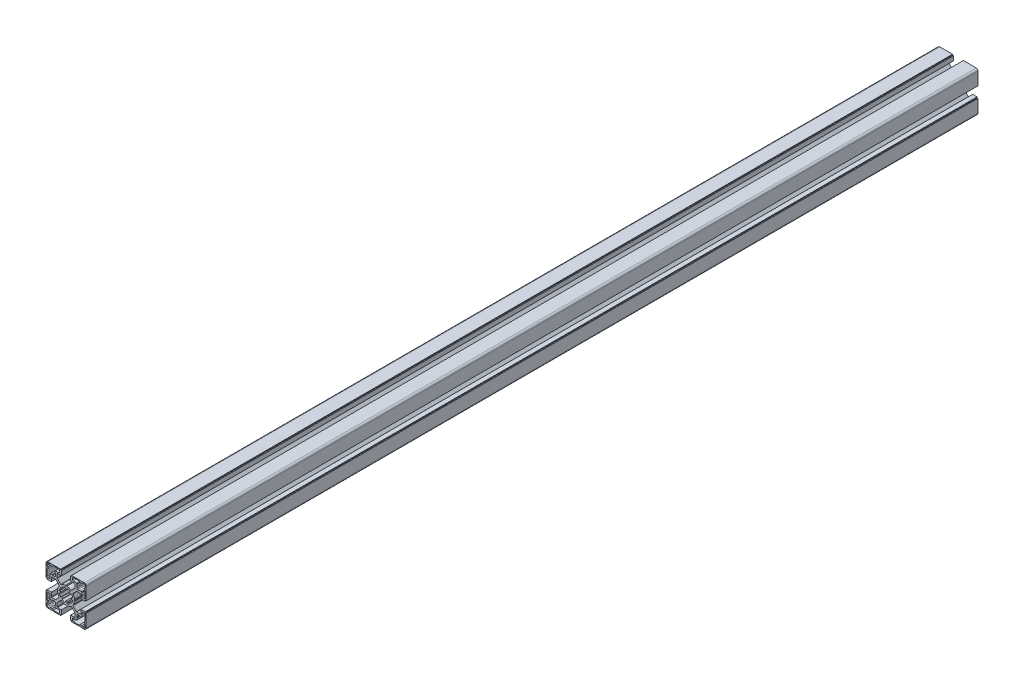
SolidWorks part; units mm, degrees
ref_plane "前视基准面" through (0, 0, 0) normal (0, 0, 1) x (1, 0, 0)
ref_plane "上视基准面" through (0, 0, 0) normal (0, 1, 0) x (1, 0, 0)
ref_plane "右视基准面" through (0, 0, 0) normal (1, 0, 0) x (0, 0, -1)
sketch "草图1" plane through (0, 0, 0) normal (0, 0, 1) x (1, 0, 0)
  line L16 (31.3495, 47.5482) -> (29.8624, 47.744)
  line L17 (28.6738, 44.8745) -> (29.8638, 43.9614)
  line L18 (28.4794, 42.577) -> (27.5663, 43.767)
  line L19 (24.6968, 42.5784) -> (24.8926, 41.0913)
  line L20 (22.9347, 41.0913) -> (23.1305, 42.5784)
  line L21 (20.2611, 43.767) -> (19.348, 42.577)
  line L22 (17.9635, 43.9614) -> (19.1536, 44.8745)
  line L23 (17.965, 47.744) -> (16.4779, 47.5482)
  line L24 (16.4779, 49.5061) -> (17.965, 49.3103)
  line L25 (19.1536, 52.1797) -> (17.9635, 53.0928)
  line L26 (19.348, 54.4773) -> (20.2611, 53.2872)
  line L27 (23.1305, 54.4758) -> (22.9347, 55.9629)
  line L28 (24.8926, 55.9629) -> (24.6968, 54.4758)
  line L29 (27.5663, 53.2872) -> (28.4794, 54.4773)
  line L30 (29.8638, 53.0928) -> (28.6738, 52.1797)
  line L31 (29.8624, 49.3103) -> (31.3495, 49.5061)
  line L32 (11.9137, 66.5271) -> (15.8137, 66.5271)
  line L33 (11.4137, 66.0271) -> (11.9137, 66.5271)
  line L34 (11.4137, 64.0271) -> (11.4137, 66.0271)
  line L35 (11.9137, 63.5271) -> (11.4137, 64.0271)
  line L36 (11.9137, 61.5271) -> (11.9137, 63.5271)
  line L37 (8.9137, 60.5271) -> (10.9137, 60.5271)
  line L38 (8.4137, 61.0271) -> (8.9137, 60.5271)
  line L39 (6.4137, 61.0271) -> (8.4137, 61.0271)
  line L40 (5.9137, 60.5271) -> (6.4137, 61.0271)
  line L41 (5.9137, 56.6271) -> (5.9137, 60.5271)
  line L42 (3.4137, 55.6271) -> (4.9137, 55.6271)
  line L43 (2.4137, 63.0271) -> (2.4137, 56.6271)
  line L44 (3.4137, 64.0271) -> (2.4137, 63.0271)
  line L45 (3.4137, 66.0271) -> (3.4137, 64.0271)
  line L46 (2.4137, 67.0271) -> (3.4137, 66.0271)
  line L47 (2.4137, 69.0271) -> (2.4137, 67.0271)
  line L48 (5.4137, 70.0271) -> (3.4137, 70.0271)
  line L49 (6.4137, 69.0271) -> (5.4137, 70.0271)
  line L50 (8.4137, 69.0271) -> (6.4137, 69.0271)
  line L51 (9.4137, 70.0271) -> (8.4137, 69.0271)
  line L52 (15.8137, 70.0271) -> (9.4137, 70.0271)
  line L53 (16.8137, 67.5271) -> (16.8137, 69.0271)
  line L54 (42.9137, 55.6271) -> (44.4137, 55.6271)
  line L55 (41.9137, 60.5271) -> (41.9137, 56.6271)
  line L56 (41.4137, 61.0271) -> (41.9137, 60.5271)
  line L57 (39.4137, 61.0271) -> (41.4137, 61.0271)
  line L58 (38.9137, 60.5271) -> (39.4137, 61.0271)
  line L59 (36.9137, 60.5271) -> (38.9137, 60.5271)
  line L60 (35.9137, 63.5271) -> (35.9137, 61.5271)
  line L61 (36.4137, 64.0271) -> (35.9137, 63.5271)
  line L62 (36.4137, 66.0271) -> (36.4137, 64.0271)
  line L63 (35.9137, 66.5271) -> (36.4137, 66.0271)
  line L64 (32.0137, 66.5271) -> (35.9137, 66.5271)
  line L65 (31.0137, 69.0271) -> (31.0137, 67.5271)
  line L66 (38.4137, 70.0271) -> (32.0137, 70.0271)
  line L67 (39.4137, 69.0271) -> (38.4137, 70.0271)
  line L68 (41.4137, 69.0271) -> (39.4137, 69.0271)
  line L69 (42.4137, 70.0271) -> (41.4137, 69.0271)
  line L70 (44.4137, 70.0271) -> (42.4137, 70.0271)
  line L71 (45.4137, 67.0271) -> (45.4137, 69.0271)
  line L72 (44.4137, 66.0271) -> (45.4137, 67.0271)
  line L73 (44.4137, 64.0271) -> (44.4137, 66.0271)
  line L74 (45.4137, 63.0271) -> (44.4137, 64.0271)
  line L75 (45.4137, 56.6271) -> (45.4137, 63.0271)
  line L76 (4.9137, 41.4271) -> (3.4137, 41.4271)
  line L77 (5.9137, 36.5271) -> (5.9137, 40.4271)
  line L78 (6.4137, 36.0271) -> (5.9137, 36.5271)
  line L79 (8.4137, 36.0271) -> (6.4137, 36.0271)
  line L80 (8.9137, 36.5271) -> (8.4137, 36.0271)
  line L81 (10.9137, 36.5271) -> (8.9137, 36.5271)
  line L82 (11.9137, 33.5271) -> (11.9137, 35.5271)
  line L83 (11.4137, 33.0271) -> (11.9137, 33.5271)
  line L84 (11.4137, 31.0271) -> (11.4137, 33.0271)
  line L85 (11.9137, 30.5271) -> (11.4137, 31.0271)
  line L86 (15.8137, 30.5271) -> (11.9137, 30.5271)
  line L87 (16.8137, 28.0271) -> (16.8137, 29.5271)
  line L88 (9.4137, 27.0271) -> (15.8137, 27.0271)
  line L89 (8.4137, 28.0271) -> (9.4137, 27.0271)
  line L90 (6.4137, 28.0271) -> (8.4137, 28.0271)
  line L91 (5.4137, 27.0271) -> (6.4137, 28.0271)
  line L92 (3.4137, 27.0271) -> (5.4137, 27.0271)
  line L93 (2.4137, 30.0271) -> (2.4137, 28.0271)
  line L94 (3.4137, 31.0271) -> (2.4137, 30.0271)
  line L95 (3.4137, 33.0271) -> (3.4137, 31.0271)
  line L96 (2.4137, 34.0271) -> (3.4137, 33.0271)
  line L97 (2.4137, 40.4271) -> (2.4137, 34.0271)
  line L98 (45.4137, 34.0271) -> (45.4137, 40.4271)
  line L99 (44.4137, 33.0271) -> (45.4137, 34.0271)
  line L100 (44.4137, 31.0271) -> (44.4137, 33.0271)
  line L101 (45.4137, 30.0271) -> (44.4137, 31.0271)
  line L102 (45.4137, 28.0271) -> (45.4137, 30.0271)
  line L103 (42.4137, 27.0271) -> (44.4137, 27.0271)
  line L104 (41.4137, 28.0271) -> (42.4137, 27.0271)
  line L105 (39.4137, 28.0271) -> (41.4137, 28.0271)
  line L106 (38.4137, 27.0271) -> (39.4137, 28.0271)
  line L107 (32.0137, 27.0271) -> (38.4137, 27.0271)
  line L108 (31.0137, 29.5271) -> (31.0137, 28.0271)
  line L109 (35.9137, 30.5271) -> (32.0137, 30.5271)
  line L110 (36.4137, 31.0271) -> (35.9137, 30.5271)
  line L111 (36.4137, 33.0271) -> (36.4137, 31.0271)
  line L112 (35.9137, 33.5271) -> (36.4137, 33.0271)
  line L113 (35.9137, 35.5271) -> (35.9137, 33.5271)
  line L114 (38.9137, 36.5271) -> (36.9137, 36.5271)
  line L115 (39.4137, 36.0271) -> (38.9137, 36.5271)
  line L116 (41.4137, 36.0271) -> (39.4137, 36.0271)
  line L117 (41.9137, 36.5271) -> (41.4137, 36.0271)
  line L118 (41.9137, 40.4271) -> (41.9137, 36.5271)
  line L119 (44.4137, 41.4271) -> (42.9137, 41.4271)
  line L120 (32.9137, 48.5271) -> (33.3794, 47.7205)
  line L121 (33.3794, 49.3337) -> (32.9137, 48.5271)
  line L122 (35.535, 58.3807) -> (31.7595, 54.6052)
  line L123 (39.9137, 58.5271) -> (35.8886, 58.5271)
  line L124 (40.4137, 53.6271) -> (40.4137, 58.0271)
  line L125 (45.4137, 53.6271) -> (40.4137, 53.6271)
  line L126 (45.4137, 54.6271) -> (45.4137, 53.6271)
  line L127 (46.4137, 54.6271) -> (45.4137, 54.6271)
  line L128 (46.4137, 69.0271) -> (46.4137, 54.6271)
  line L129 (30.0137, 71.0271) -> (44.4137, 71.0271)
  line L130 (30.0137, 70.0271) -> (30.0137, 71.0271)
  line L131 (29.0137, 70.0271) -> (30.0137, 70.0271)
  line L132 (29.0137, 65.0271) -> (29.0137, 70.0271)
  line L133 (33.4137, 65.0271) -> (29.0137, 65.0271)
  line L134 (33.9137, 60.502) -> (33.9137, 64.5271)
  line L135 (29.9918, 56.3729) -> (33.7672, 60.1484)
  line L136 (23.9137, 57.5271) -> (24.7203, 57.9928)
  line L137 (23.1071, 57.9928) -> (23.9137, 57.5271)
  line L138 (14.0601, 60.1484) -> (17.8356, 56.3729)
  line L139 (13.9137, 64.5271) -> (13.9137, 60.502)
  line L140 (18.8137, 65.0271) -> (14.4137, 65.0271)
  line L141 (18.8137, 70.0271) -> (18.8137, 65.0271)
  line L142 (17.8137, 70.0271) -> (18.8137, 70.0271)
  line L143 (17.8137, 71.0271) -> (17.8137, 70.0271)
  line L144 (3.4137, 71.0271) -> (17.8137, 71.0271)
  line L145 (1.4137, 54.6271) -> (1.4137, 69.0271)
  line L146 (2.4137, 54.6271) -> (1.4137, 54.6271)
  line L147 (2.4137, 53.6271) -> (2.4137, 54.6271)
  line L148 (7.4137, 53.6271) -> (2.4137, 53.6271)
  line L149 (7.4137, 58.0271) -> (7.4137, 53.6271)
  line L150 (11.9388, 58.5271) -> (7.9137, 58.5271)
  line L151 (16.0679, 54.6052) -> (12.2924, 58.3807)
  line L152 (14.9137, 48.5271) -> (14.448, 49.3337)
  line L153 (14.448, 47.7205) -> (14.9137, 48.5271)
  line L154 (12.2924, 38.6736) -> (16.0679, 42.449)
  line L155 (7.9137, 38.5271) -> (11.9388, 38.5271)
  line L156 (7.4137, 43.4271) -> (7.4137, 39.0271)
  line L157 (2.4137, 43.4271) -> (7.4137, 43.4271)
  line L158 (2.4137, 42.4271) -> (2.4137, 43.4271)
  line L159 (1.4137, 42.4271) -> (2.4137, 42.4271)
  line L160 (1.4137, 28.0271) -> (1.4137, 42.4271)
  line L161 (17.8137, 26.0271) -> (3.4137, 26.0271)
  line L162 (17.8137, 27.0271) -> (17.8137, 26.0271)
  line L163 (18.8137, 27.0271) -> (17.8137, 27.0271)
  line L164 (18.8137, 32.0271) -> (18.8137, 27.0271)
  line L165 (14.4137, 32.0271) -> (18.8137, 32.0271)
  line L166 (13.9137, 36.5522) -> (13.9137, 32.5271)
  line L167 (17.8356, 40.6813) -> (14.0601, 36.9058)
  line L168 (23.9137, 39.5271) -> (23.1071, 39.0614)
  line L169 (24.7203, 39.0614) -> (23.9137, 39.5271)
  line L170 (33.7672, 36.9058) -> (29.9918, 40.6813)
  line L171 (33.9137, 32.5271) -> (33.9137, 36.5522)
  line L172 (29.0137, 32.0271) -> (33.4137, 32.0271)
  line L173 (29.0137, 27.0271) -> (29.0137, 32.0271)
  line L174 (30.0137, 27.0271) -> (29.0137, 27.0271)
  line L175 (30.0137, 26.0271) -> (30.0137, 27.0271)
  line L176 (44.4137, 26.0271) -> (30.0137, 26.0271)
  line L177 (46.4137, 42.4271) -> (46.4137, 28.0271)
  line L178 (45.4137, 42.4271) -> (46.4137, 42.4271)
  line L179 (45.4137, 43.4271) -> (45.4137, 42.4271)
  line L180 (40.4137, 43.4271) -> (45.4137, 43.4271)
  line L181 (40.4137, 39.0271) -> (40.4137, 43.4271)
  line L182 (35.8886, 38.5271) -> (39.9137, 38.5271)
  line L183 (31.7595, 42.449) -> (35.535, 38.6736)
  arc A0 (29.8624, 47.744) -> (29.8624, 49.3103) centre (23.9137, 48.5271) ccw
  arc A1 (29.8638, 43.9614) -> (31.3495, 47.5482) centre (23.9137, 48.5271) ccw
  arc A2 (27.5663, 43.767) -> (28.6738, 44.8745) centre (23.9137, 48.5271) ccw
  arc A3 (24.8926, 41.0913) -> (28.4794, 42.577) centre (23.9137, 48.5271) ccw
  arc A4 (23.1305, 42.5784) -> (24.6968, 42.5784) centre (23.9137, 48.5271) ccw
  arc A5 (19.348, 42.577) -> (22.9347, 41.0913) centre (23.9137, 48.5271) ccw
  arc A6 (19.1536, 44.8745) -> (20.2611, 43.767) centre (23.9137, 48.5271) ccw
  arc A7 (16.4779, 47.5482) -> (17.9635, 43.9614) centre (23.9137, 48.5271) ccw
  arc A8 (17.965, 49.3103) -> (17.965, 47.744) centre (23.9137, 48.5271) ccw
  arc A9 (17.9635, 53.0928) -> (16.4779, 49.5061) centre (23.9137, 48.5271) ccw
  arc A10 (20.2611, 53.2872) -> (19.1536, 52.1797) centre (23.9137, 48.5271) ccw
  arc A11 (22.9347, 55.9629) -> (19.348, 54.4773) centre (23.9137, 48.5271) ccw
  arc A12 (24.6968, 54.4758) -> (23.1305, 54.4758) centre (23.9137, 48.5271) ccw
  arc A13 (28.4794, 54.4773) -> (24.8926, 55.9629) centre (23.9137, 48.5271) ccw
  arc A14 (28.6738, 52.1797) -> (27.5663, 53.2872) centre (23.9137, 48.5271) ccw
  arc A15 (31.3495, 49.5061) -> (29.8638, 53.0928) centre (23.9137, 48.5271) ccw
  arc A16 (10.9137, 60.5271) -> (11.9137, 61.5271) centre (10.9137, 61.5271) ccw
  arc A17 (4.9137, 55.6271) -> (5.9137, 56.6271) centre (4.9137, 56.6271) ccw
  arc A18 (2.4137, 56.6271) -> (3.4137, 55.6271) centre (3.4137, 56.6271) ccw
  arc A19 (3.4137, 70.0271) -> (2.4137, 69.0271) centre (3.4137, 69.0271) ccw
  arc A20 (16.8137, 69.0271) -> (15.8137, 70.0271) centre (15.8137, 69.0271) ccw
  arc A21 (15.8137, 66.5271) -> (16.8137, 67.5271) centre (15.8137, 67.5271) ccw
  arc A22 (44.4137, 55.6271) -> (45.4137, 56.6271) centre (44.4137, 56.6271) ccw
  arc A23 (41.9137, 56.6271) -> (42.9137, 55.6271) centre (42.9137, 56.6271) ccw
  arc A24 (35.9137, 61.5271) -> (36.9137, 60.5271) centre (36.9137, 61.5271) ccw
  arc A25 (31.0137, 67.5271) -> (32.0137, 66.5271) centre (32.0137, 67.5271) ccw
  arc A26 (32.0137, 70.0271) -> (31.0137, 69.0271) centre (32.0137, 69.0271) ccw
  arc A27 (45.4137, 69.0271) -> (44.4137, 70.0271) centre (44.4137, 69.0271) ccw
  arc A28 (3.4137, 41.4271) -> (2.4137, 40.4271) centre (3.4137, 40.4271) ccw
  arc A29 (5.9137, 40.4271) -> (4.9137, 41.4271) centre (4.9137, 40.4271) ccw
  arc A30 (11.9137, 35.5271) -> (10.9137, 36.5271) centre (10.9137, 35.5271) ccw
  arc A31 (16.8137, 29.5271) -> (15.8137, 30.5271) centre (15.8137, 29.5271) ccw
  arc A32 (15.8137, 27.0271) -> (16.8137, 28.0271) centre (15.8137, 28.0271) ccw
  arc A33 (2.4137, 28.0271) -> (3.4137, 27.0271) centre (3.4137, 28.0271) ccw
  arc A34 (45.4137, 40.4271) -> (44.4137, 41.4271) centre (44.4137, 40.4271) ccw
  arc A35 (44.4137, 27.0271) -> (45.4137, 28.0271) centre (44.4137, 28.0271) ccw
  arc A36 (31.0137, 28.0271) -> (32.0137, 27.0271) centre (32.0137, 28.0271) ccw
  arc A37 (32.0137, 30.5271) -> (31.0137, 29.5271) centre (32.0137, 29.5271) ccw
  arc A38 (36.9137, 36.5271) -> (35.9137, 35.5271) centre (36.9137, 35.5271) ccw
  arc A39 (42.9137, 41.4271) -> (41.9137, 40.4271) centre (42.9137, 40.4271) ccw
  arc A40 (31.7031, 43.0888) -> (31.7595, 42.449) centre (32.1131, 42.8026) ccw
  arc A41 (31.7031, 43.0888) -> (33.3794, 47.7205) centre (23.9137, 48.5271) ccw
  arc A42 (33.3794, 49.3337) -> (31.7031, 53.9654) centre (23.9137, 48.5271) ccw
  arc A43 (31.7595, 54.6052) -> (31.7031, 53.9654) centre (32.1131, 54.2516) ccw
  arc A44 (35.8886, 58.5271) -> (35.535, 58.3807) centre (35.8886, 58.0271) ccw
  arc A45 (40.4137, 58.0271) -> (39.9137, 58.5271) centre (39.9137, 58.0271) ccw
  arc A46 (46.4137, 69.0271) -> (44.4137, 71.0271) centre (44.4137, 69.0271) ccw
  arc A47 (33.9137, 64.5271) -> (33.4137, 65.0271) centre (33.4137, 64.5271) ccw
  arc A48 (33.7672, 60.1484) -> (33.9137, 60.502) centre (33.4137, 60.502) ccw
  arc A49 (29.352, 56.3165) -> (29.9918, 56.3729) centre (29.6382, 56.7265) ccw
  arc A50 (29.352, 56.3165) -> (24.7203, 57.9928) centre (23.9137, 48.5271) ccw
  arc A51 (23.1071, 57.9928) -> (18.4754, 56.3165) centre (23.9137, 48.5271) ccw
  arc A52 (17.8356, 56.3729) -> (18.4754, 56.3165) centre (18.1892, 56.7265) ccw
  arc A53 (13.9137, 60.502) -> (14.0601, 60.1484) centre (14.4137, 60.502) ccw
  arc A54 (14.4137, 65.0271) -> (13.9137, 64.5271) centre (14.4137, 64.5271) ccw
  arc A55 (3.4137, 71.0271) -> (1.4137, 69.0271) centre (3.4137, 69.0271) ccw
  arc A56 (7.9137, 58.5271) -> (7.4137, 58.0271) centre (7.9137, 58.0271) ccw
  arc A57 (12.2924, 58.3807) -> (11.9388, 58.5271) centre (11.9388, 58.0271) ccw
  arc A58 (16.1243, 53.9654) -> (16.0679, 54.6052) centre (15.7143, 54.2516) ccw
  arc A59 (16.1243, 53.9654) -> (14.448, 49.3337) centre (23.9137, 48.5271) ccw
  arc A60 (14.448, 47.7205) -> (16.1243, 43.0888) centre (23.9137, 48.5271) ccw
  arc A61 (16.0679, 42.449) -> (16.1243, 43.0888) centre (15.7143, 42.8026) ccw
  arc A62 (11.9388, 38.5271) -> (12.2924, 38.6736) centre (11.9388, 39.0271) ccw
  arc A63 (7.4137, 39.0271) -> (7.9137, 38.5271) centre (7.9137, 39.0271) ccw
  arc A64 (1.4137, 28.0271) -> (3.4137, 26.0271) centre (3.4137, 28.0271) ccw
  arc A65 (13.9137, 32.5271) -> (14.4137, 32.0271) centre (14.4137, 32.5271) ccw
  arc A66 (14.0601, 36.9058) -> (13.9137, 36.5522) centre (14.4137, 36.5522) ccw
  arc A67 (18.4754, 40.7377) -> (17.8356, 40.6813) centre (18.1892, 40.3277) ccw
  arc A68 (18.4754, 40.7377) -> (23.1071, 39.0614) centre (23.9137, 48.5271) ccw
  arc A69 (24.7203, 39.0614) -> (29.352, 40.7377) centre (23.9137, 48.5271) ccw
  arc A70 (29.9918, 40.6813) -> (29.352, 40.7377) centre (29.6382, 40.3277) ccw
  arc A71 (33.9137, 36.5522) -> (33.7672, 36.9058) centre (33.4137, 36.5522) ccw
  arc A72 (33.4137, 32.0271) -> (33.9137, 32.5271) centre (33.4137, 32.5271) ccw
  arc A73 (44.4137, 26.0271) -> (46.4137, 28.0271) centre (44.4137, 28.0271) ccw
  arc A74 (39.9137, 38.5271) -> (40.4137, 39.0271) centre (39.9137, 39.0271) ccw
  arc A75 (35.535, 38.6736) -> (35.8886, 38.5271) centre (35.8886, 39.0271) ccw
extrude "拉伸1" add sketch "草图1" along normal blind 1000
